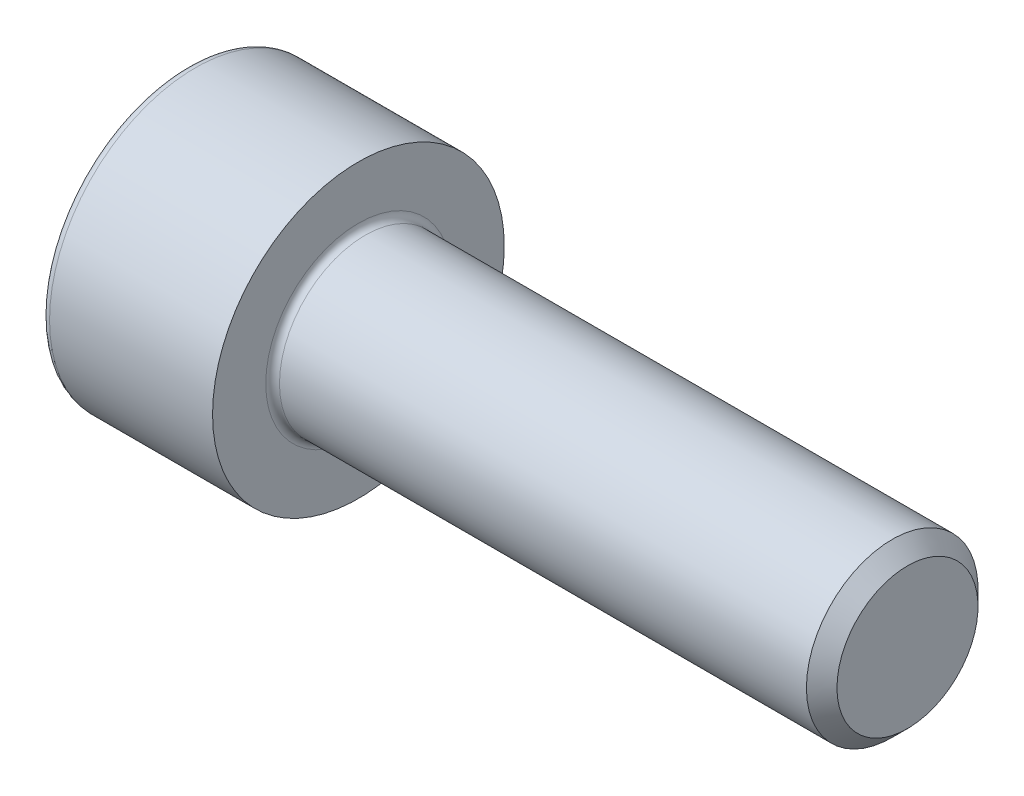
SolidWorks part; units mm, degrees
ref_plane "Plane1" through (0, 0, 0) normal (0, 0, 1) x (1, 0, 0)
ref_plane "Plane2" through (0, 0, 0) normal (0, 1, 0) x (1, 0, 0)
ref_plane "Plane3" through (0, 0, 0) normal (1, 0, 0) x (0, 0, -1)
sketch "BodySke" plane through (0, 0, 0) normal (0, 0, 1) x (1, 0, 0)
  line L0 (0, 0) -> (0, 4.25)
  line L1 (0, 4.25) -> (5, 4.25)
  line L2 (5, 4.25) -> (5, 2.5)
  line L3 (5, 2.5) -> (20.555, 2.5)
  line L4 (21, 2.055) -> (21, 0)
  line L5 (21, 0) -> (0, 0)
  line L6 (-31.75, 0) -> (127, 0) construction
  line L8 (21, 2.055) -> (20.555, 2.5)
  line L10 (21, -2.055) -> (20.555, -2.5) construction
  line L11 (5.8, 9.525) -> (5.8, 3.175) construction
  line L12 (5, 9.525) -> (5, 3.175) construction
  line L13 (-39, 9.525) -> (-39, 3.175) construction
  dimension "Diameter" = 5
  dimension "Head_ht" = 5
  dimension "Length" = 16
  dimension "Body_ch_ang" = 45
  dimension "Head_dia" = 8.5
  dimension "Minor_dia" = 4.11
  dimension "Advance" = 0.8
  dimension "Thread_nom" = 16
  dimension "Thread_length" = 60
revolve "Base-Revolve" add sketch "BodySke"
cosmetic thread "ThreadCosmetic" [suppressed]
fillet "Fillet1" radius 0.2 1 edges at (5, 0, 2.5)
fillet "Fillet2" radius 0.25 1 edges at (0, 0, 4.25)
sketch "Sketch2" plane through (0, 0, 0) normal (0, 0, 1) x (1, 0, 0)
  line L0 (0, 2.042) -> (2.5, 2.042)
  line L1 (2.5, 2.042) -> (3.6789, 0)
  line L2 (-31.75, 0) -> (127, 0) construction
  line L3 (3.6789, 0) -> (0, 0)
  line L4 (0, 0) -> (0, 2.042)
  line L6 (0, 0) -> (47.625, 0) construction
  dimension "D1" = 2.042
  dimension "D2" = 60
  dimension "Depth" = 2.5
revolve "Hex-PreBroach" cut sketch "Sketch2" angle 360 about L6
sketch "Sketch3" plane through (0, 0, 0) normal (-1, 0, 0) x (0, 0.5, 0.866)
  line L0 (1.1789, 2.042) -> (-1.1789, 2.042)
  line L1 (-1.1789, 2.042) -> (-2.3579, 0)
  line L2 (1.1789, 2.042) -> (2.3579, 0)
  line L3 (1.1789, -2.042) -> (2.3579, 0)
  line L4 (1.1789, -2.042) -> (-1.1789, -2.042)
  line L5 (-1.1789, -2.042) -> (-2.3579, 0)
  dimension "D1" = 2.042
  dimension "D2" = 2.042
  dimension "Hex_size" = 4.084
extrude "Hex" cut sketch "Sketch3" against normal blind 2.5
sketch "ThdSchSke" plane through (0, 0, 0) normal (0, 0, 1) x (1, 0, 0)
  line L0 (7.4, -2.055) -> (7.0884, -2.5)
  line L1 (7.4, -2.055) -> (7.7116, -2.5)
  line L2 (7.7116, -2.5) -> (7.7116, -3.125)
  line L3 (-3.175, 0) -> (5.1513, 0) construction
  line L4 (0, 4) -> (0, -4) construction
  line L5 (7.7116, -3.125) -> (7.0884, -3.125)
  line L6 (7.0884, -3.125) -> (7.0884, -2.5)
  dimension "Thread_minor" = 4.11
  dimension "Diameter" = 5
  dimension "Start" = 7.4
  dimension "SideAngle" = 55
  dimension "VeeAngle" = 70
  dimension "Overcut" = 6.25
revolve "ThreadSchematic" [suppressed] cut sketch "ThdSchSke" angle 360 about L3
pattern_linear "ThdSchPat" [suppressed]
equation "\"D2@Sketch3\" = \"Hex_size@Sketch3\" / 2"
equation "\"D1@Sketch3\" = \"Hex_size@Sketch3\" / 2"
equation "\"D1@Sketch2\" = \"Hex_size@Sketch3\" / 2"
equation "\"Thread_minor@ThreadCosmetic\"  =  \"Minor_dia@BodySke\""
equation "\"Depth@Sketch2\" =  \"Key_eng@Hex\""
equation "\"Thread_length@ThreadCosmetic\" = ((sgn( (\"Length@BodySke\" - \"Advance@BodySke\" * 3.0) - \"Thread_nom@BodySke\" )-1)*( (\"Length@BodySke\" - \"Advance@BodySke\" * 3.0) - \"Thread_nom@BodySke\" ))/-2+ \"Thread_nom@BodySke\""
equation "\"Thread_minor@ThdSchSke\" = \"Minor_dia@BodySke\""
equation "\"Diameter@ThdSchSke\" = \"Diameter@BodySke\""
equation "\"Overcut@ThdSchSke\" = \"Diameter@BodySke\" * 1.25"
equation "\"Start@ThdSchSke\" = \"Head_ht@BodySke\" + \"Length@BodySke\" - \"Thread_length@ThreadCosmetic\"  '---Non-countersunk---"
equation "\"Num_threads@ThdSchPat\" = int( \"Thread_length@ThreadCosmetic\" / \"Advance@BodySke\" + 0.999 )  + 1"
equation "\"Advance@ThdSchPat\" = \"Thread_length@ThreadCosmetic\" /  (\"Num_threads@ThdSchPat\" - 1) 'relax it"
equation "\"Num_threads@ThdSchPat\" = \"Num_threads@ThdSchPat\" - sgn( \"Num_threads@ThdSchPat\" - 1) '---chamfered tips only---"
